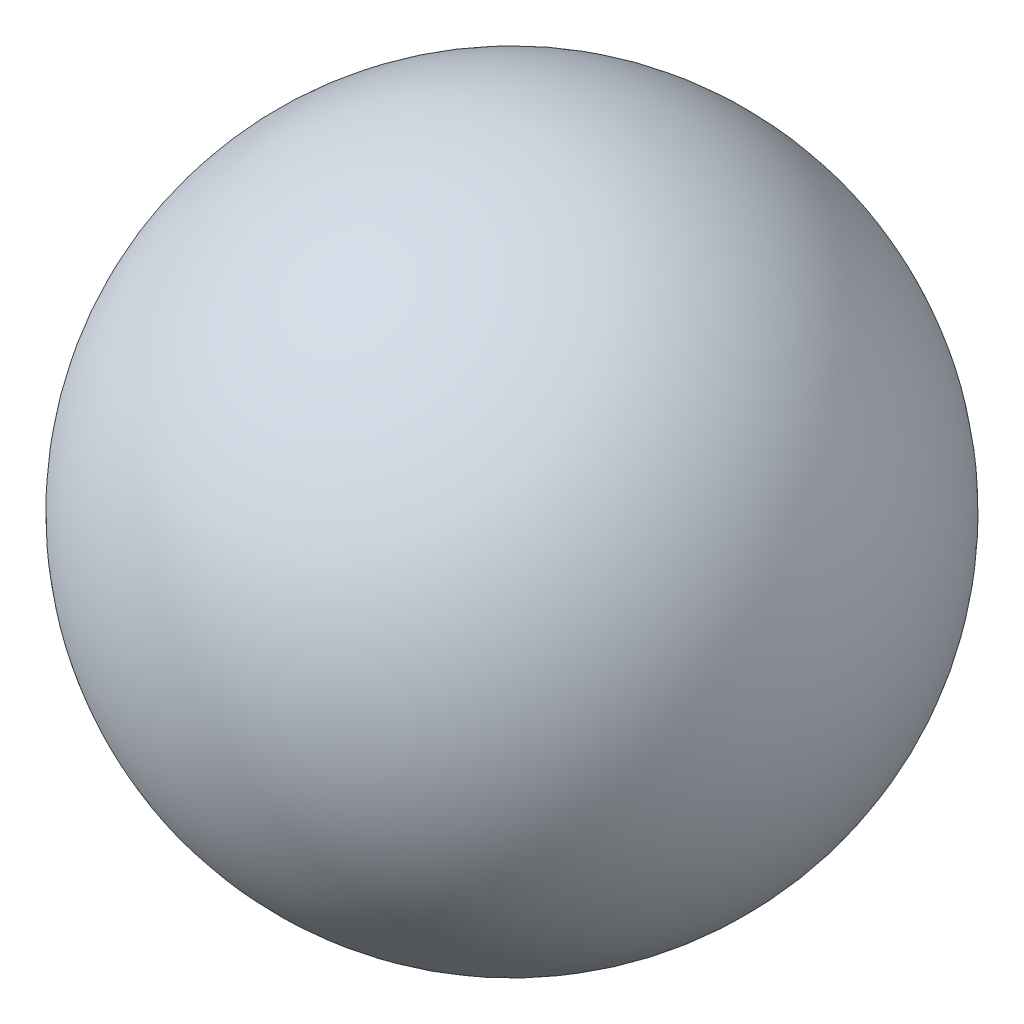
SolidWorks part; units mm, degrees
ref_plane "Front Plane" through (0, 0, 0) normal (0, 0, 1) x (1, 0, 0)
ref_plane "Top Plane" through (0, 0, 0) normal (0, 1, 0) x (1, 0, 0)
ref_plane "Right Plane" through (0, 0, 0) normal (1, 0, 0) x (0, 0, -1)
sketch "Sketch1" plane through (0, 0, 0) normal (0, 1, 0) x (1, 0, 0)
  line L0 (0, 6.35) -> (0, -6.35)
  arc A0 (0, -6.35) -> (0, 6.35) centre (0, 0) ccw
  dimension "D1" = 12.7
revolve "Revolve1" add sketch "Sketch1" angle 360 about L0
